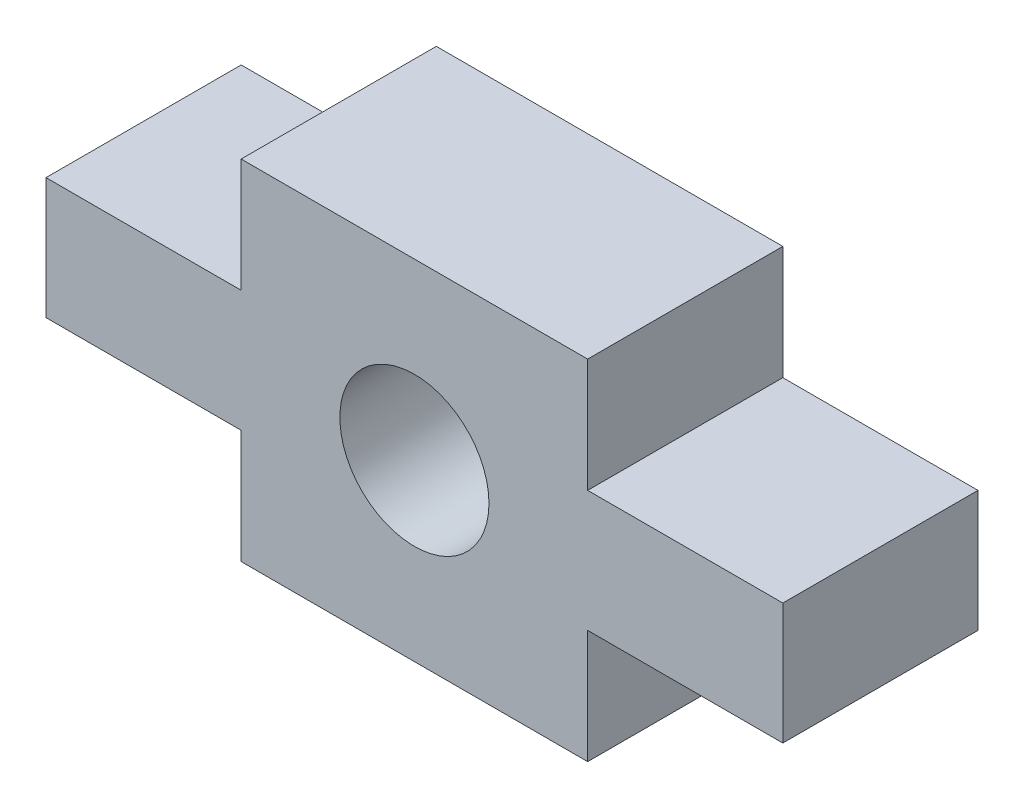
SolidWorks part; units mm, degrees
ref_plane "Front Plane" through (0, 0, 0) normal (0, 0, 1) x (1, 0, 0)
ref_plane "Top Plane" through (0, 0, 0) normal (0, 1, 0) x (1, 0, 0)
ref_plane "Right Plane" through (0, 0, 0) normal (1, 0, 0) x (0, 0, -1)
sketch "Sketch1" plane through (0, 0, 0) normal (0, 0, 1) x (1, 0, 0)
  line L0 (0, 6) -> (0, 3) construction
  line L1 (0, -55) -> (0, 55) construction
  line L2 (0, 3) -> (5.15, 3) construction
  line L3 (5.15, 3) -> (5.15, 0) construction
  line L4 (55, 0) -> (-55, 0) construction
  line L5 (5.15, 0) -> (14.093, 0) construction
  line L6 (14.093, 0) -> (14.093, 3) construction
  line L7 (14.093, 3) -> (19.243, 3) construction
  line L8 (19.243, 3) -> (19.243, 6) construction
  line L9 (19.243, 6) -> (14.093, 6) construction
  line L10 (14.093, 6) -> (14.093, 9) construction
  line L11 (14.093, 9) -> (5.15, 9) construction
  line L12 (5.15, 9) -> (5.15, 6) construction
  line L13 (5.15, 6) -> (0, 6) construction
  line L14 (-0.1, 6.1) -> (-0.1, 2.9)
  line L15 (-0.1, 2.9) -> (5.05, 2.9)
  line L16 (5.05, 2.9) -> (5.05, -0.1)
  line L17 (5.05, -0.1) -> (14.193, -0.1)
  line L18 (14.193, -0.1) -> (14.193, 2.9)
  line L19 (14.193, 2.9) -> (19.343, 2.9)
  line L20 (19.343, 2.9) -> (19.343, 6.1)
  line L21 (19.343, 6.1) -> (14.193, 6.1)
  line L22 (14.193, 6.1) -> (14.193, 9.1)
  line L23 (14.193, 9.1) -> (5.05, 9.1)
  line L24 (5.05, 9.1) -> (5.05, 6.1)
  line L25 (5.05, 6.1) -> (-0.1, 6.1)
  dimension "D1" = 3
  dimension "D2" = 5.15
  dimension "D3" = 9
  dimension "D4" = 8.943
  dimension "D5" = 0.1
extrude "Boss-Extrude1" add sketch "Sketch1" along normal blind 5.15
sketch "Sketch2" plane through (0, 0, 5.15) normal (0, 0, 1) x (1, 0, 0)
  line L0 (19.243, 4.5) -> (-1.5028, 4.5) construction
  line L1 (19.243, 3) -> (19.243, 6) construction
  line L2 (9.6215, 9) -> (9.6215, -2.7997) construction
  line L3 (14.093, 9) -> (5.15, 9) construction
  circle A0 centre (9.6215, 4.5) radius 2.0675 construction
  circle A1 centre (9.6215, 4.5) radius 1.9675
  point P8 (9.6215, 4.5)
  dimension "D1" = 0.1
extrude "Cut-Extrude1" cut sketch "Sketch2" against normal through all
